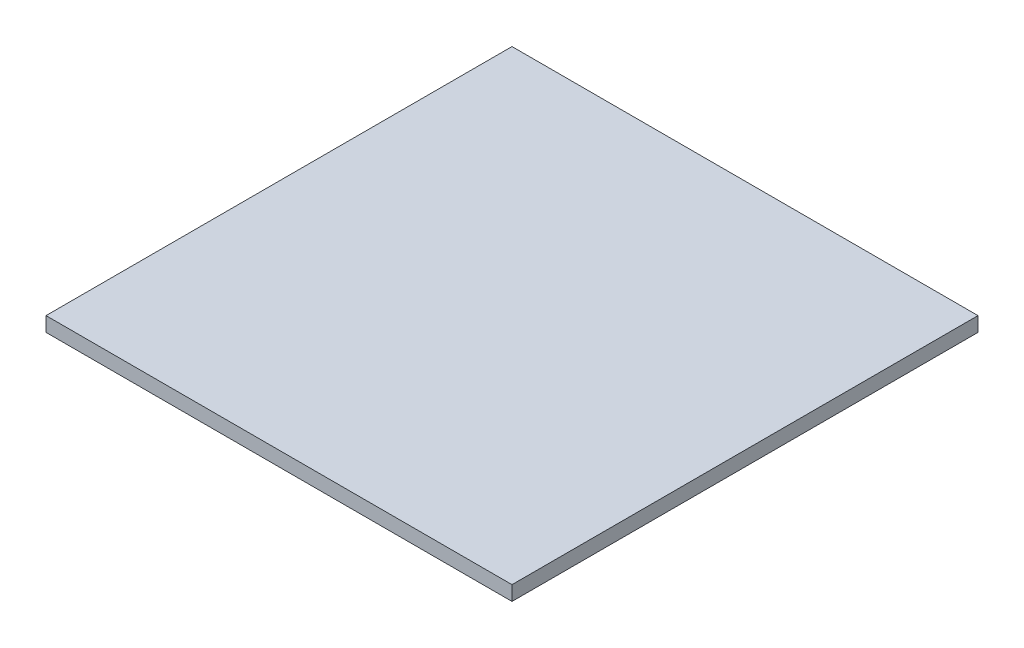
SolidWorks part; units mm, degrees
ref_plane "Front Plane" through (0, 0, 0) normal (0, 0, 1) x (1, 0, 0)
ref_plane "Top Plane" through (0, 0, 0) normal (0, 1, 0) x (1, 0, 0)
ref_plane "Right Plane" through (0, 0, 0) normal (1, 0, 0) x (0, 0, -1)
sketch "Sketch1" plane through (0, 0, 0) normal (0, 1, 0) x (1, 0, 0)
  line L1 (0, 0) -> (101.6, 0)
  line L2 (0, 0) -> (0, 101.6)
  line L3 (0, 101.6) -> (101.6, 101.6)
  line L4 (101.6, 0) -> (101.6, 101.6)
  dimension "D1" = 101.6
  dimension "D2" = 101.6
extrude "Boss-Extrude1" add sketch "Sketch1" along normal blind 3.175
